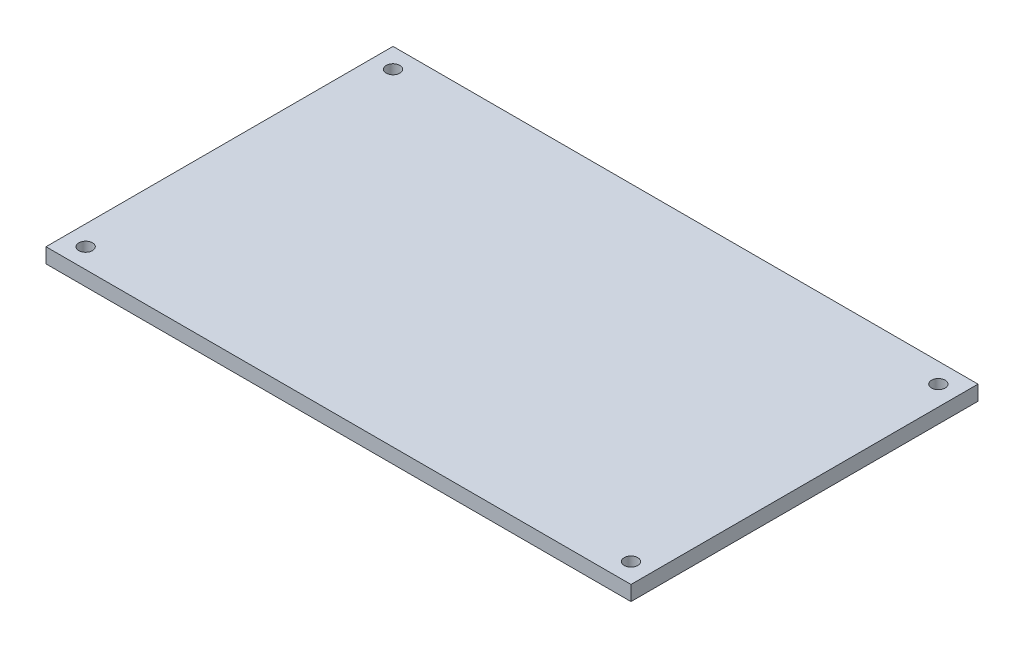
SolidWorks part; units mm, degrees
ref_plane "Front Plane" through (0, 0, 0) normal (0, 0, 1) x (1, 0, 0)
ref_plane "Top Plane" through (0, 0, 0) normal (0, 1, 0) x (1, 0, 0)
ref_plane "Right Plane" through (0, 0, 0) normal (1, 0, 0) x (0, 0, -1)
sketch "Sketch1" plane through (0, 0, 0) normal (0, 1, 0) x (1, 0, 0)
  line L1 (-59, -35) -> (59, -35)
  line L2 (-59, -35) -> (-59, 35)
  line L3 (-59, 35) -> (59, 35)
  line L4 (59, -35) -> (59, 35)
  line L5 (-59, -35) -> (59, 35) construction
  line L6 (-59, 35) -> (59, -35) construction
  circle A0 centre (-55, 31) radius 1.375
  circle A1 centre (55, 31) radius 1.375
  circle A2 centre (55, -31) radius 1.375
  circle A3 centre (-55, -31) radius 1.375
  point P0 (0, 0)
  dimension "D5" = 2.75
  dimension "D6" = 2.75
  dimension "D9" = 2.75
  dimension "D10" = 2.75
  dimension "D1" = 118
  dimension "D2" = 70
  dimension "D3" = 4
  dimension "D4" = 4
  dimension "D7" = 4
  dimension "D8" = 4
  dimension "D11" = 4
  dimension "D12" = 4
  dimension "D13" = 4
  dimension "D14" = 4
extrude "Boss-Extrude1" add sketch "Sketch1" along normal blind 3
